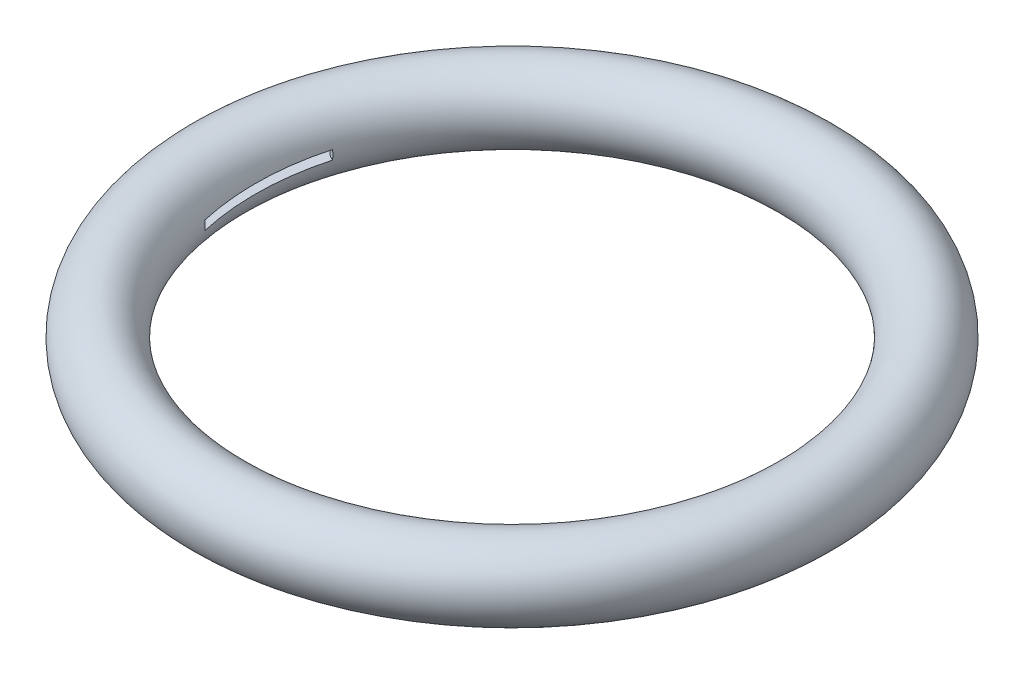
SolidWorks part; units mm, degrees
material "ABS"
ref_plane "Front Plane" through (0, 0, 0) normal (0, 0, 1) x (1, 0, 0)
ref_plane "Top Plane" through (0, 0, 0) normal (0, 1, 0) x (1, 0, 0)
ref_plane "Right Plane" through (0, 0, 0) normal (1, 0, 0) x (0, 0, -1)
sketch "Sketch1" plane through (0, 0, 0) normal (0, 0, 1) x (1, 0, 0)
  line L0 (0, 3.175) -> (0, -3.175) construction
  line L1 (0, 3.175) -> (101.6, 3.175) construction
  line L2 (101.6, 3.175) -> (101.6, -3.175) construction
  line L3 (101.6, -3.175) -> (0, -3.175) construction
  circle A1 centre (101.6, 0) radius 12.7
  point P6 (0, 0)
  dimension "D1" = 25.4
  dimension "D2" = 101.6
  dimension "D3" = 6.35
revolve "Revolve1" add sketch "Sketch1" angle 360 about L0
sketch "Sketch3" plane through (0, 0, 0) normal (0, 1, 0) x (1, 0, 0)
  line L0 (0, 38.1) -> (0, -38.1) construction
  line L1 (0, -19.05) -> (0, 19.05) construction
  line L2 (-93.3256, 19.05) -> (93.3256, 19.05) construction
  line L3 (93.3256, 19.05) -> (93.3256, -19.05) construction
  line L4 (93.3256, -19.05) -> (-93.3256, -19.05) construction
  line L5 (-93.3256, -19.05) -> (-93.3256, 19.05) construction
  line L6 (0, 142.903) -> (0, -142.903) construction
  line L7 (-19.05, -93.3256) -> (19.05, -93.3256) construction
  circle A0 centre (0, 0) radius 107.95
  arc A4 (27.7576, -91.1158) -> (91.1158, -27.7576) centre (0, 0) ccw
  arc A5 (-81.6387, 23.6682) -> (81.6387, 23.6682) centre (0, -200.025) cw
  arc A6 (19.6045, -84.2669) -> (84.2669, -19.6045) centre (93.3256, -93.3256) cw
  arc A7 (-84.2669, -19.6045) -> (-19.6045, -84.2669) centre (-93.3256, -93.3256) cw
  arc A8 (89.8026, 31.75) -> (-89.8026, 31.75) centre (0, 0) ccw
  arc A9 (-91.1158, -27.7576) -> (-27.7576, -91.1158) centre (0, 0) ccw
  arc A10 (84.2669, -19.6045) -> (91.1158, -27.7576) centre (85.0414, -25.9071) cw
  arc A11 (27.7576, -91.1158) -> (19.6045, -84.2669) centre (25.9071, -85.0414) cw
  arc A12 (-27.7576, -91.1158) -> (-19.6045, -84.2669) centre (-25.9071, -85.0414) ccw
  arc A13 (-84.2669, -19.6045) -> (-91.1158, -27.7576) centre (-85.0414, -25.9071) ccw
  arc A14 (81.6387, 23.6682) -> (89.8026, 31.75) centre (83.8157, 29.6333) ccw
  arc A15 (-81.6387, 23.6682) -> (-89.8026, 31.75) centre (-83.8157, 29.6333) cw
  point P7 (0, 0)
  point P10 (0, 38.1)
  point P11 (0, 0)
  point P14 (0, 19.05)
  point P15 (0, 38.1)
  point P20 (0, 0)
  point P24 (0, -93.3256)
  dimension "D1" = 76.2
  dimension "D2" = 190.5
  dimension "D3" = 215.9
  dimension "D4" = 38.1
  dimension "D6" = 6.35
  dimension "D5" = 38.1
extrude "Cut-Extrude1" cut sketch "Sketch3" against normal mid plane 3.175 contours A5 A14 A8 A15
